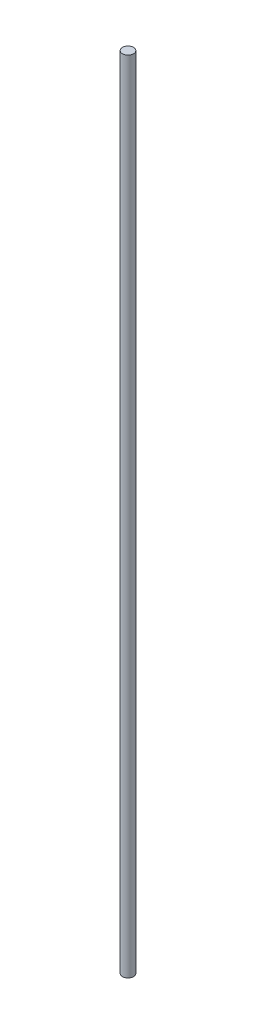
SolidWorks part; units mm, degrees
ref_plane "Front Plane" through (0, 0, 0) normal (0, 0, 1) x (1, 0, 0)
ref_plane "Top Plane" through (0, 0, 0) normal (0, 1, 0) x (1, 0, 0)
ref_plane "Right Plane" through (0, 0, 0) normal (1, 0, 0) x (0, 0, -1)
sketch "Sketch1" plane through (0, 0, 0) normal (0, 1, 0) x (1, 0, 0)
  circle A0 centre (0, 0) radius 1.5875
  dimension "D1" = 3.175
extrude "Boss-Extrude1" add sketch "Sketch1" along normal blind 228.6
